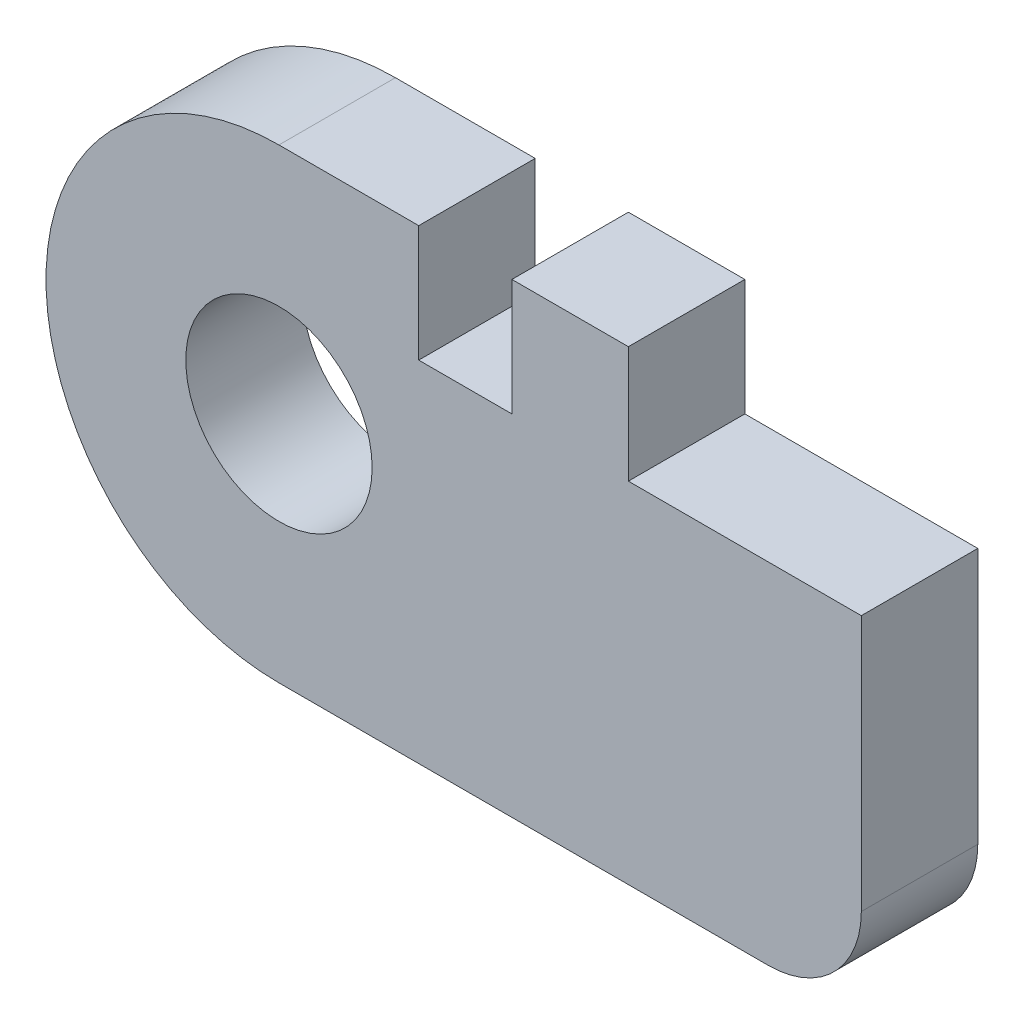
SolidWorks part; units mm, degrees
ref_plane "Front Plane" through (0, 0, 0) normal (0, 0, 1) x (1, 0, 0)
ref_plane "Top Plane" through (0, 0, 0) normal (0, 1, 0) x (1, 0, 0)
ref_plane "Right Plane" through (0, 0, 0) normal (1, 0, 0) x (0, 0, -1)
sketch "Sketch1" plane through (0, 0, 0) normal (0, 0, 1) x (1, 0, 0)
  line L0 (22.5, 5) -> (22.5, -6)
  line L1 (18.5, -10) -> (-2.5, -10)
  line L2 (12.5, 10) -> (12.5, 5)
  line L3 (3.5, 10) -> (-2.5, 10)
  line L4 (7.5, 5) -> (7.5, 10)
  line L5 (7.5, 5) -> (3.5, 5)
  line L7 (7.5, 10) -> (12.5, 10)
  line L9 (3.5, 10) -> (3.5, 5)
  line L21 (12.5, 5) -> (22.5, 5)
  arc A0 (-2.5, 10) -> (-2.5, -10) centre (-2.5, 0) ccw
  circle A1 centre (-2.5, 0) radius 4
  arc A2 (22.5, -6) -> (18.5, -10) centre (18.5, -6) cw
  dimension "D1" = 4
extrude "Boss-Extrude4" add sketch "Sketch1" along normal blind 5
